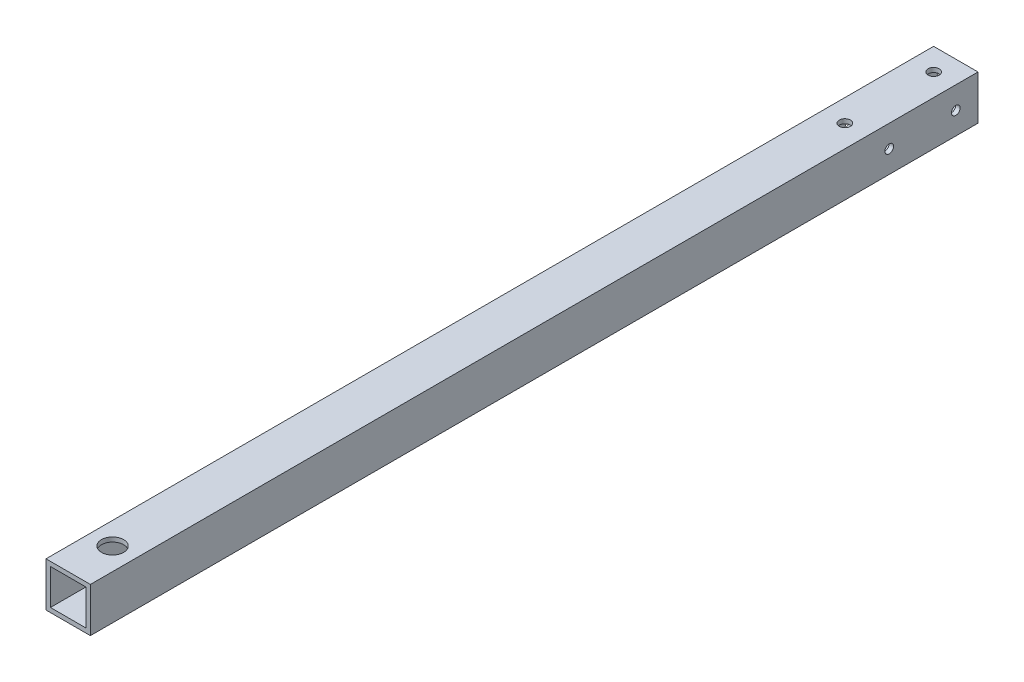
SolidWorks part; units mm, degrees
ref_plane "Front Plane" through (0, 0, 0) normal (0, 0, 1) x (1, 0, 0)
ref_plane "Top Plane" through (0, 0, 0) normal (0, 1, 0) x (1, 0, 0)
ref_plane "Right Plane" through (0, 0, 0) normal (1, 0, 0) x (0, 0, -1)
sketch "Sketch1" plane through (0, 0, 0) normal (0, 0, 1) x (1, 0, 0)
  line L1 (-12.7, -12.7) -> (12.7, -12.7)
  line L2 (-12.7, -12.7) -> (-12.7, 12.7)
  line L3 (-12.7, 12.7) -> (12.7, 12.7)
  line L4 (12.7, -12.7) -> (12.7, 12.7)
  line L5 (-12.7, -12.7) -> (12.7, 12.7) construction
  line L6 (-12.7, 12.7) -> (12.7, -12.7) construction
  point P0 (0, 0)
  dimension "D1" = 25.4
  dimension "D2" = 25.4
extrude "Extrude-Thin1" add sketch "Sketch1" along normal mid plane 508 thin contours L3 L4 L1 L2 thin type one direction reverse wall 2.54
sketch "Sketch2" plane through (0, 12.7, 0) normal (0, 1, 0) x (1, 0, 0)
  line L0 (-12.7, 254) -> (12.7, 254) construction
  circle A0 centre (0, 241.3) radius 3.175
  circle A1 centre (0, 190.5) radius 3.175
  dimension "D1" = 6.35
  dimension "D2" = 6.35
  dimension "D3" = 12.7
  dimension "D4" = 50.8
extrude "Cut-Extrude1" cut sketch "Sketch2" against normal through all
sketch "Sketch3" plane through (0, 12.7, 0) normal (0, 1, 0) x (1, 0, 0)
  line L0 (-12.7, -254) -> (12.7, -254) construction
  circle A0 centre (0, -228.6) radius 6.35
  dimension "D1" = 12.7
  dimension "D2" = 25.4
extrude "Cut-Extrude2" cut sketch "Sketch3" against normal through all
sketch "Sketch4" plane through (-12.7, 0, 0) normal (-1, 0, 0) x (0, 0, 1)
  line L0 (254, -12.7) -> (254, 12.7) construction
  line L1 (-254, -12.7) -> (-254, 12.7) construction
  line L2 (-254, 0) -> (254, 0) construction
  circle A0 centre (-241.3, 0) radius 2.4892
  circle A1 centre (-203.2, 0) radius 2.4892
  dimension "D1" = 4.9784
  dimension "D2" = 4.9784
  dimension "D3" = 12.7
  dimension "D4" = 38.1
extrude "Cut-Extrude3" cut sketch "Sketch4" against normal through all
